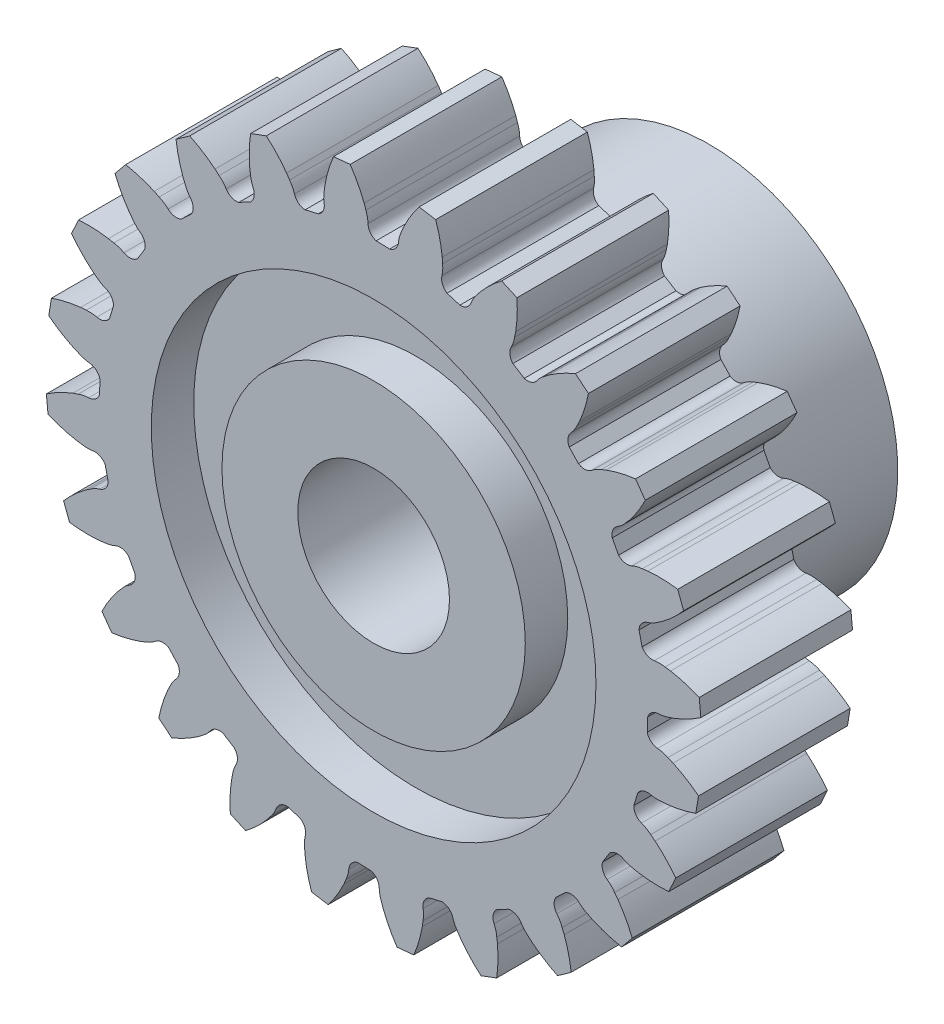
SolidWorks part; units mm, degrees
ref_plane "Front Plane" through (0, 0, 0) normal (0, 0, 1) x (1, 0, 0)
ref_plane "Top Plane" through (0, 0, 0) normal (0, 1, 0) x (1, 0, 0)
ref_plane "Right Plane" through (0, 0, 0) normal (1, 0, 0) x (0, 0, -1)
sketch "Model" plane through (0, 0, 0) normal (0, 0, 1) x (1, 0, 0)
  line L0 (68.8089, 76.1004) -> (68.9498, 76.2835)
  line L1 (69.8603, 77.1457) -> (70.4994, 76.8553)
  line L2 (70.4489, 75.6024) -> (70.4037, 75.3758)
  line L3 (70.3295, 74.3844) -> (70.807, 74.0867)
  line L4 (71.6645, 74.5899) -> (71.8481, 74.7303)
  line L5 (72.9507, 75.3274) -> (73.4928, 74.8815)
  line L6 (73.1197, 73.6844) -> (73.0174, 73.4772)
  line L7 (72.6892, 72.5387) -> (73.0734, 72.1276)
  line L8 (74.0318, 72.3918) -> (74.2455, 72.4798)
  line L9 (75.4651, 72.7713) -> (75.8734, 72.2002)
  line L10 (75.2031, 71.1405) -> (75.0507, 70.9668)
  line L11 (74.4907, 70.1453) -> (74.7554, 69.6487)
  line L12 (75.7496, 69.6558) -> (75.9788, 69.6856)
  line L13 (77.2322, 69.6514) -> (77.4788, 68.9942)
  line L14 (76.5571, 68.144) -> (76.3649, 68.0157)
  line L15 (75.6114, 67.3671) -> (75.7386, 66.819)
  line L16 (76.7007, 66.5685) -> (76.9298, 66.5379)
  line L17 (78.1317, 66.1805) -> (78.1998, 65.4818)
  line L18 (77.0894, 64.8992) -> (76.8706, 64.825)
  line L19 (75.9749, 64.3935) -> (75.9559, 63.8312)
  line L20 (76.8204, 63.3402) -> (77.0338, 63.2514)
  line L21 (78.1022, 62.5951) -> (77.9871, 61.9026)
  line L22 (76.7638, 61.6271) -> (76.5332, 61.6121)
  line L23 (75.5564, 61.4272) -> (75.3925, 60.8889)
  line L24 (76.1004, 60.1909) -> (76.2835, 60.0499)
  line L25 (77.1457, 59.1394) -> (76.8553, 58.5003)
  line L26 (75.6024, 58.5509) -> (75.3758, 58.5961)
  line L27 (74.3844, 58.6703) -> (74.0867, 58.1927)
  line L28 (74.5899, 57.3353) -> (74.7303, 57.1517)
  line L29 (75.3274, 56.0491) -> (74.8815, 55.5069)
  line L30 (73.6844, 55.8801) -> (73.4772, 55.9824)
  line L31 (72.5387, 56.3106) -> (72.1276, 55.9264)
  line L32 (72.3918, 54.9679) -> (72.4798, 54.7543)
  line L33 (72.7713, 53.5347) -> (72.2002, 53.1264)
  line L34 (71.1405, 53.7966) -> (70.9668, 53.9491)
  line L35 (70.1453, 54.509) -> (69.6487, 54.2443)
  line L36 (69.6558, 53.2502) -> (69.6856, 53.021)
  line L37 (69.6514, 51.7675) -> (68.9942, 51.521)
  line L38 (68.144, 52.4426) -> (68.0157, 52.6349)
  line L39 (67.3671, 53.3883) -> (66.819, 53.2612)
  line L40 (66.5685, 52.299) -> (66.5379, 52.07)
  line L41 (66.1805, 50.8681) -> (65.4818, 50.8)
  line L42 (64.8992, 51.9103) -> (64.825, 52.1292)
  line L43 (64.3935, 53.0249) -> (63.8312, 53.0439)
  line L44 (63.3402, 52.1794) -> (63.2514, 51.966)
  line L45 (62.5951, 50.8976) -> (61.9026, 51.0127)
  line L46 (61.6271, 52.236) -> (61.6121, 52.4666)
  line L47 (61.4272, 53.4434) -> (60.8889, 53.6073)
  line L48 (60.1909, 52.8994) -> (60.0499, 52.7162)
  line L49 (59.1394, 51.8541) -> (58.5003, 52.1445)
  line L50 (58.5509, 53.3974) -> (58.5961, 53.624)
  line L51 (58.6703, 54.6154) -> (58.1927, 54.9131)
  line L52 (57.3353, 54.4099) -> (57.1517, 54.2695)
  line L53 (56.0491, 53.6723) -> (55.5069, 54.1183)
  line L54 (55.8801, 55.3154) -> (55.9824, 55.5226)
  line L55 (56.3106, 56.461) -> (55.9264, 56.8721)
  line L56 (54.9679, 56.608) -> (54.7543, 56.5199)
  line L57 (53.5347, 56.2285) -> (53.1264, 56.7996)
  line L58 (53.7966, 57.8593) -> (53.9491, 58.033)
  line L59 (54.509, 58.8545) -> (54.2443, 59.351)
  line L60 (53.2502, 59.344) -> (53.021, 59.3142)
  line L61 (51.7675, 59.3483) -> (51.521, 60.0056)
  line L62 (52.4426, 60.8558) -> (52.6349, 60.9841)
  line L63 (53.3883, 61.6327) -> (53.2612, 62.1808)
  line L64 (52.299, 62.4313) -> (52.07, 62.4618)
  line L65 (50.8681, 62.8192) -> (50.8, 63.5179)
  line L66 (51.9103, 64.1006) -> (52.1292, 64.1748)
  line L67 (53.0249, 64.6063) -> (53.0439, 65.1686)
  line L68 (52.1794, 65.6596) -> (51.966, 65.7484)
  line L69 (50.8976, 66.4047) -> (51.0127, 67.0972)
  line L70 (52.236, 67.3726) -> (52.4666, 67.3876)
  line L71 (53.4434, 67.5726) -> (53.6073, 68.1109)
  line L72 (52.8994, 68.8089) -> (52.7162, 68.9498)
  line L73 (51.8541, 69.8603) -> (52.1445, 70.4994)
  line L74 (53.3974, 70.4489) -> (53.624, 70.4037)
  line L75 (54.6154, 70.3295) -> (54.9131, 70.807)
  line L76 (54.4099, 71.6645) -> (54.2695, 71.8481)
  line L77 (53.6723, 72.9507) -> (54.1183, 73.4928)
  line L78 (55.3154, 73.1197) -> (55.5226, 73.0174)
  line L79 (56.461, 72.6892) -> (56.8721, 73.0734)
  line L80 (56.608, 74.0318) -> (56.5199, 74.2455)
  line L81 (56.2285, 75.4651) -> (56.7996, 75.8734)
  line L82 (57.8593, 75.2031) -> (58.033, 75.0507)
  line L83 (58.8545, 74.4907) -> (59.351, 74.7554)
  line L84 (59.344, 75.7496) -> (59.3142, 75.9788)
  line L85 (59.3483, 77.2322) -> (60.0056, 77.4788)
  line L86 (60.8558, 76.5571) -> (60.9841, 76.3649)
  line L87 (61.6327, 75.6114) -> (62.1808, 75.7386)
  line L88 (62.4313, 76.7007) -> (62.4618, 76.9298)
  line L89 (62.8192, 78.1317) -> (63.5179, 78.1998)
  line L90 (64.1006, 77.0894) -> (64.1748, 76.8706)
  line L91 (64.6063, 75.9749) -> (65.1686, 75.9559)
  line L92 (65.6596, 76.8204) -> (65.7484, 77.0338)
  line L93 (66.4047, 78.1022) -> (67.0972, 77.9871)
  line L94 (67.3726, 76.7638) -> (67.3876, 76.5332)
  line L95 (67.5726, 75.5564) -> (68.1109, 75.3925)
  circle A0 centre (64.4999, 64.4999) radius 3.175
  arc A1 (68.1109, 75.3925) -> (68.5816, 75.7143) centre (68.1248, 75.8773) ccw
  arc A2 (68.8089, 76.1004) -> (68.5816, 75.7143) centre (69.8211, 75.2447) ccw
  arc A3 (69.8603, 77.1457) -> (68.9498, 76.2835) centre (73.153, 72.7567) ccw
  arc A4 (70.4489, 75.6024) -> (70.4994, 76.8553) centre (65.0277, 76.4487) ccw
  arc A5 (70.2623, 74.9506) -> (70.4037, 75.3758) centre (69.0933, 75.5754) ccw
  arc A6 (70.2623, 74.9506) -> (70.3295, 74.3844) centre (70.6856, 74.7137) ccw
  arc A7 (70.807, 74.0867) -> (71.345, 74.2757) centre (70.9459, 74.5514) ccw
  arc A8 (71.6645, 74.5899) -> (71.345, 74.2757) centre (72.4207, 73.5013) ccw
  arc A9 (72.9507, 75.3274) -> (71.8481, 74.7303) centre (74.9952, 70.2358) ccw
  arc A10 (73.1197, 73.6844) -> (73.4928, 74.8815) centre (68.1023, 75.9049) ccw
  arc A11 (72.7708, 73.1031) -> (73.0174, 73.4772) centre (71.8033, 74.0091) ccw
  arc A12 (72.7708, 73.1031) -> (72.6892, 72.5387) centre (73.1183, 72.7647) ccw
  arc A13 (73.0734, 72.1276) -> (73.6419, 72.171) centre (73.3278, 72.5406) ccw
  arc A14 (74.0318, 72.3918) -> (73.6419, 72.171) centre (74.4806, 71.1446) ccw
  arc A15 (75.4651, 72.7713) -> (74.2455, 72.4798) centre (76.1221, 67.324) ccw
  arc A16 (75.2031, 71.1405) -> (75.8734, 72.2002) centre (70.9314, 74.5839) ccw
  arc A17 (74.7156, 70.6693) -> (75.0507, 70.9668) centre (74.0157, 71.7948) ccw
  arc A18 (74.7156, 70.6693) -> (74.4907, 70.1453) centre (74.9638, 70.2525) ccw
  arc A19 (74.7554, 69.6487) -> (75.3158, 69.5435) centre (75.1081, 69.9818) ccw
  arc A20 (75.7496, 69.6558) -> (75.3158, 69.5435) centre (75.8603, 68.3349) ccw
  arc A21 (77.2322, 69.6514) -> (75.9788, 69.6856) centre (76.457, 64.2197) ccw
  arc A22 (76.5571, 68.144) -> (77.4788, 68.9942) centre (73.3222, 72.5757) ccw
  arc A23 (75.9643, 67.815) -> (76.3649, 68.0157) centre (75.5795, 69.0834) ccw
  arc A24 (75.9643, 67.815) -> (75.6114, 67.3671) centre (76.0961, 67.3482) ccw
  arc A25 (75.7386, 66.819) -> (76.2527, 66.5722) centre (76.1655, 67.0494) ccw
  arc A26 (76.7007, 66.5685) -> (76.2527, 66.5722) centre (76.4658, 65.264) ccw
  arc A27 (78.1317, 66.1805) -> (76.9298, 66.5379) centre (75.9771, 61.1345) ccw
  arc A28 (77.0894, 64.8992) -> (78.1998, 65.4818) centre (75.1117, 70.0171) ccw
  arc A29 (76.4317, 64.7348) -> (76.8706, 64.825) centre (76.3883, 66.0596) ccw
  arc A30 (76.4317, 64.7348) -> (75.9749, 64.3935) centre (76.4382, 64.2498) ccw
  arc A31 (75.9559, 63.8312) -> (76.3886, 63.4598) centre (76.4278, 63.9432) ccw
  arc A32 (76.8204, 63.3402) -> (76.3886, 63.4598) centre (76.2558, 62.1409) ccw
  arc A33 (78.1022, 62.5951) -> (77.0338, 63.2514) centre (74.715, 58.2786) ccw
  arc A34 (76.7638, 61.6271) -> (77.9871, 61.9026) centre (76.1781, 67.0826) ccw
  arc A35 (76.0859, 61.6387) -> (76.5332, 61.6121) centre (76.3869, 62.9295) ccw
  arc A36 (76.0859, 61.6387) -> (75.5564, 61.4272) centre (75.9667, 61.1685) ccw
  arc A37 (75.3925, 60.8889) -> (75.7143, 60.4182) centre (75.8773, 60.875) ccw
  arc A38 (76.1004, 60.1909) -> (75.7143, 60.4182) centre (75.2447, 59.1787) ccw
  arc A39 (77.1457, 59.1394) -> (76.2835, 60.0499) centre (72.7567, 55.8468) ccw
  arc A40 (75.6024, 58.5509) -> (76.8553, 58.5003) centre (76.4487, 63.972) ccw
  arc A41 (74.9506, 58.7375) -> (75.3758, 58.5961) centre (75.5754, 59.9065) ccw
  arc A42 (74.9506, 58.7375) -> (74.3844, 58.6703) centre (74.7137, 58.3142) ccw
  arc A43 (74.0867, 58.1927) -> (74.2757, 57.6548) centre (74.5514, 58.0538) ccw
  arc A44 (74.5899, 57.3353) -> (74.2757, 57.6548) centre (73.5013, 56.579) ccw
  arc A45 (75.3274, 56.0491) -> (74.7303, 57.1517) centre (70.2358, 54.0046) ccw
  arc A46 (73.6844, 55.8801) -> (74.8815, 55.5069) centre (75.9049, 60.8975) ccw
  arc A47 (73.1031, 56.229) -> (73.4772, 55.9824) centre (74.0091, 57.1964) ccw
  arc A48 (73.1031, 56.229) -> (72.5387, 56.3106) centre (72.7647, 55.8814) ccw
  arc A49 (72.1276, 55.9264) -> (72.171, 55.3578) centre (72.5406, 55.6719) ccw
  arc A50 (72.3918, 54.9679) -> (72.171, 55.3578) centre (71.1446, 54.5192) ccw
  arc A51 (72.7713, 53.5347) -> (72.4798, 54.7543) centre (67.324, 52.8777) ccw
  arc A52 (71.1405, 53.7966) -> (72.2002, 53.1264) centre (74.5839, 58.0684) ccw
  arc A53 (70.6693, 54.2841) -> (70.9668, 53.9491) centre (71.7948, 54.9841) ccw
  arc A54 (70.6693, 54.2841) -> (70.1453, 54.509) centre (70.2525, 54.036) ccw
  arc A55 (69.6487, 54.2443) -> (69.5435, 53.6839) centre (69.9818, 53.8917) ccw
  arc A56 (69.6558, 53.2502) -> (69.5435, 53.6839) centre (68.3349, 53.1395) ccw
  arc A57 (69.6514, 51.7675) -> (69.6856, 53.021) centre (64.2197, 52.5427) ccw
  arc A58 (68.144, 52.4426) -> (68.9942, 51.521) centre (72.5757, 55.6776) ccw
  arc A59 (67.815, 53.0355) -> (68.0157, 52.6349) centre (69.0834, 53.4203) ccw
  arc A60 (67.815, 53.0355) -> (67.3671, 53.3883) centre (67.3482, 52.9037) ccw
  arc A61 (66.819, 53.2612) -> (66.5722, 52.7471) centre (67.0494, 52.8343) ccw
  arc A62 (66.5685, 52.299) -> (66.5722, 52.7471) centre (65.264, 52.534) ccw
  arc A63 (66.1805, 50.8681) -> (66.5379, 52.07) centre (61.1345, 53.0227) ccw
  arc A64 (64.8992, 51.9103) -> (65.4818, 50.8) centre (70.0171, 53.888) ccw
  arc A65 (64.7348, 52.5681) -> (64.825, 52.1292) centre (66.0596, 52.6115) ccw
  arc A66 (64.7348, 52.5681) -> (64.3935, 53.0249) centre (64.2498, 52.5616) ccw
  arc A67 (63.8312, 53.0439) -> (63.4598, 52.6112) centre (63.9432, 52.5719) ccw
  arc A68 (63.3402, 52.1794) -> (63.4598, 52.6112) centre (62.1409, 52.744) ccw
  arc A69 (62.5951, 50.8976) -> (63.2514, 51.966) centre (58.2786, 54.2848) ccw
  arc A70 (61.6271, 52.236) -> (61.9026, 51.0127) centre (67.0826, 52.8216) ccw
  arc A71 (61.6387, 52.9139) -> (61.6121, 52.4666) centre (62.9295, 52.6129) ccw
  arc A72 (61.6387, 52.9139) -> (61.4272, 53.4434) centre (61.1685, 53.0331) ccw
  arc A73 (60.8889, 53.6073) -> (60.4182, 53.2855) centre (60.875, 53.1225) ccw
  arc A74 (60.1909, 52.8994) -> (60.4182, 53.2855) centre (59.1787, 53.7551) ccw
  arc A75 (59.1394, 51.8541) -> (60.0499, 52.7162) centre (55.8468, 56.243) ccw
  arc A76 (58.5509, 53.3974) -> (58.5003, 52.1445) centre (63.972, 52.5511) ccw
  arc A77 (58.7375, 54.0492) -> (58.5961, 53.624) centre (59.9065, 53.4244) ccw
  arc A78 (58.7375, 54.0492) -> (58.6703, 54.6154) centre (58.3142, 54.286) ccw
  arc A79 (58.1927, 54.9131) -> (57.6548, 54.724) centre (58.0538, 54.4483) ccw
  arc A80 (57.3353, 54.4099) -> (57.6548, 54.724) centre (56.579, 55.4984) ccw
  arc A81 (56.0491, 53.6723) -> (57.1517, 54.2695) centre (54.0046, 58.764) ccw
  arc A82 (55.8801, 55.3154) -> (55.5069, 54.1183) centre (60.8975, 53.0949) ccw
  arc A83 (56.229, 55.8967) -> (55.9824, 55.5226) centre (57.1964, 54.9906) ccw
  arc A84 (56.229, 55.8967) -> (56.3106, 56.461) centre (55.8814, 56.235) ccw
  arc A85 (55.9264, 56.8721) -> (55.3578, 56.8288) centre (55.6719, 56.4592) ccw
  arc A86 (54.9679, 56.608) -> (55.3578, 56.8288) centre (54.5192, 57.8552) ccw
  arc A87 (53.5347, 56.2285) -> (54.7543, 56.5199) centre (52.8777, 61.6758) ccw
  arc A88 (53.7966, 57.8593) -> (53.1264, 56.7996) centre (58.0684, 54.4159) ccw
  arc A89 (54.2841, 58.3305) -> (53.9491, 58.033) centre (54.9841, 57.2049) ccw
  arc A90 (54.2841, 58.3305) -> (54.509, 58.8545) centre (54.036, 58.7473) ccw
  arc A91 (54.2443, 59.351) -> (53.6839, 59.4563) centre (53.8917, 59.018) ccw
  arc A92 (53.2502, 59.344) -> (53.6839, 59.4563) centre (53.1395, 60.6648) ccw
  arc A93 (51.7675, 59.3483) -> (53.021, 59.3142) centre (52.5428, 64.7801) ccw
  arc A94 (52.4426, 60.8558) -> (51.521, 60.0056) centre (55.6776, 56.4241) ccw
  arc A95 (53.0355, 61.1848) -> (52.6349, 60.9841) centre (53.4203, 59.9164) ccw
  arc A96 (53.0355, 61.1848) -> (53.3883, 61.6327) centre (52.9037, 61.6516) ccw
  arc A97 (53.2612, 62.1808) -> (52.7471, 62.4276) centre (52.8343, 61.9504) ccw
  arc A98 (52.299, 62.4313) -> (52.7471, 62.4276) centre (52.534, 63.7358) ccw
  arc A99 (50.8681, 62.8192) -> (52.07, 62.4618) centre (53.0227, 67.8653) ccw
  arc A100 (51.9103, 64.1006) -> (50.8, 63.5179) centre (53.888, 58.9826) ccw
  arc A101 (52.5681, 64.2649) -> (52.1292, 64.1748) centre (52.6115, 62.9402) ccw
  arc A102 (52.5681, 64.2649) -> (53.0249, 64.6063) centre (52.5616, 64.7499) ccw
  arc A103 (53.0439, 65.1686) -> (52.6112, 65.54) centre (52.5719, 65.0565) ccw
  arc A104 (52.1794, 65.6596) -> (52.6112, 65.54) centre (52.744, 66.8588) ccw
  arc A105 (50.8976, 66.4047) -> (51.966, 65.7484) centre (54.2848, 70.7211) ccw
  arc A106 (52.236, 67.3726) -> (51.0127, 67.0972) centre (52.8216, 61.9172) ccw
  arc A107 (52.9139, 67.3611) -> (52.4666, 67.3876) centre (52.6129, 66.0702) ccw
  arc A108 (52.9139, 67.3611) -> (53.4434, 67.5726) centre (53.0331, 67.8313) ccw
  arc A109 (53.6073, 68.1109) -> (53.2855, 68.5816) centre (53.1225, 68.1248) ccw
  arc A110 (52.8994, 68.8089) -> (53.2855, 68.5816) centre (53.7551, 69.8211) ccw
  arc A111 (51.8541, 69.8603) -> (52.7162, 68.9498) centre (56.243, 73.153) ccw
  arc A112 (53.3974, 70.4489) -> (52.1445, 70.4994) centre (52.5511, 65.0277) ccw
  arc A113 (54.0492, 70.2623) -> (53.624, 70.4037) centre (53.4244, 69.0933) ccw
  arc A114 (54.0492, 70.2623) -> (54.6154, 70.3295) centre (54.286, 70.6856) ccw
  arc A115 (54.9131, 70.807) -> (54.724, 71.345) centre (54.4483, 70.9459) ccw
  arc A116 (54.4099, 71.6645) -> (54.724, 71.345) centre (55.4984, 72.4207) ccw
  arc A117 (53.6723, 72.9507) -> (54.2695, 71.8481) centre (58.764, 74.9952) ccw
  arc A118 (55.3154, 73.1197) -> (54.1183, 73.4928) centre (53.0949, 68.1023) ccw
  arc A119 (55.8967, 72.7708) -> (55.5226, 73.0174) centre (54.9906, 71.8033) ccw
  arc A120 (55.8967, 72.7708) -> (56.461, 72.6892) centre (56.235, 73.1183) ccw
  arc A121 (56.8721, 73.0734) -> (56.8288, 73.6419) centre (56.4592, 73.3278) ccw
  arc A122 (56.608, 74.0318) -> (56.8288, 73.6419) centre (57.8552, 74.4806) ccw
  arc A123 (56.2285, 75.4651) -> (56.5199, 74.2455) centre (61.6758, 76.1221) ccw
  arc A124 (57.8593, 75.2031) -> (56.7996, 75.8734) centre (54.4159, 70.9314) ccw
  arc A125 (58.3305, 74.7156) -> (58.033, 75.0507) centre (57.2049, 74.0157) ccw
  arc A126 (58.3305, 74.7156) -> (58.8545, 74.4907) centre (58.7473, 74.9638) ccw
  arc A127 (59.351, 74.7554) -> (59.4563, 75.3158) centre (59.018, 75.1081) ccw
  arc A128 (59.344, 75.7496) -> (59.4563, 75.3158) centre (60.6648, 75.8603) ccw
  arc A129 (59.3483, 77.2322) -> (59.3142, 75.9788) centre (64.7801, 76.457) ccw
  arc A130 (60.8558, 76.5571) -> (60.0056, 77.4788) centre (56.4241, 73.3222) ccw
  arc A131 (61.1848, 75.9643) -> (60.9841, 76.3649) centre (59.9164, 75.5795) ccw
  arc A132 (61.1848, 75.9643) -> (61.6327, 75.6114) centre (61.6516, 76.0961) ccw
  arc A133 (62.1808, 75.7386) -> (62.4276, 76.2527) centre (61.9504, 76.1655) ccw
  arc A134 (62.4313, 76.7007) -> (62.4276, 76.2527) centre (63.7358, 76.4658) ccw
  arc A135 (62.8192, 78.1317) -> (62.4618, 76.9298) centre (67.8653, 75.9771) ccw
  arc A136 (64.1006, 77.0894) -> (63.5179, 78.1998) centre (58.9826, 75.1117) ccw
  arc A137 (64.2649, 76.4317) -> (64.1748, 76.8706) centre (62.9402, 76.3883) ccw
  arc A138 (64.2649, 76.4317) -> (64.6063, 75.9749) centre (64.7499, 76.4382) ccw
  arc A139 (65.1686, 75.9559) -> (65.54, 76.3886) centre (65.0565, 76.4278) ccw
  arc A140 (65.6596, 76.8204) -> (65.54, 76.3886) centre (66.8588, 76.2558) ccw
  arc A141 (66.4047, 78.1022) -> (65.7484, 77.0338) centre (70.7211, 74.715) ccw
  arc A142 (67.3726, 76.7638) -> (67.0972, 77.9871) centre (61.9172, 76.1781) ccw
  arc A143 (67.3611, 76.0859) -> (67.3876, 76.5332) centre (66.0702, 76.3869) ccw
  arc A144 (67.3611, 76.0859) -> (67.5726, 75.5564) centre (67.8313, 75.9667) ccw
extrude "Boss-Extrude1" add sketch "Model" along normal blind 6.35
sketch "Sketch2" plane through (0, 0, 6.35) normal (0, 0, 1) x (1, 0, 0)
  circle A0 centre (64.4999, 64.4999) radius 9.3091
  circle A1 centre (64.4999, 64.4999) radius 6.35
  dimension "D1" = 18.6182
  dimension "D2" = 12.7
extrude "Cut-Extrude1" cut sketch "Sketch2" against normal blind 1.778
sketch "Sketch3" plane through (0, 0, 0) normal (0, 0, -1) x (-1, 0, 0)
  circle A0 centre (-64.4999, 64.4999) radius 9.3091
extrude "Cut-Extrude2" cut sketch "Sketch3" against normal blind 1.778
sketch "Sketch4" plane through (0, 0, 1.778) normal (0, 0, -1) x (-1, 0, 0)
  circle A0 centre (-64.4999, 64.4999) radius 7.8994
  circle A1 centre (-64.4999, 64.4999) radius 3.175
  dimension "D1" = 15.7988
extrude "Boss-Extrude2" add sketch "Sketch4" along normal blind 9.4742
